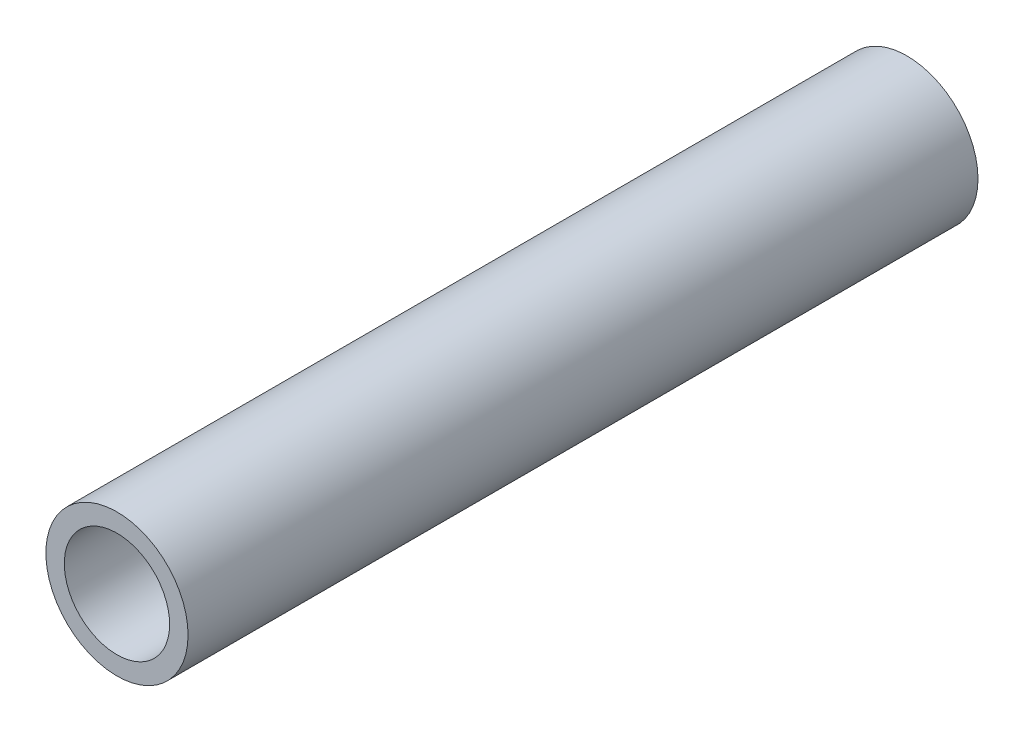
SolidWorks part; units mm, degrees
material "1060 Alloy"
ref_plane "Front Plane" through (0, 0, 0) normal (0, 0, 1) x (1, 0, 0)
ref_plane "Top Plane" through (0, 0, 0) normal (0, 1, 0) x (1, 0, 0)
ref_plane "Right Plane" through (0, 0, 0) normal (1, 0, 0) x (0, 0, -1)
sketch "Sketch1" plane through (0, 0, 0) normal (0, 0, 1) x (1, 0, 0)
  circle A0 centre (0, 0) radius 1.35
  circle A1 centre (0, 0) radius 1
extrude "Boss-Extrude1" add sketch "Sketch1" along normal blind 15
